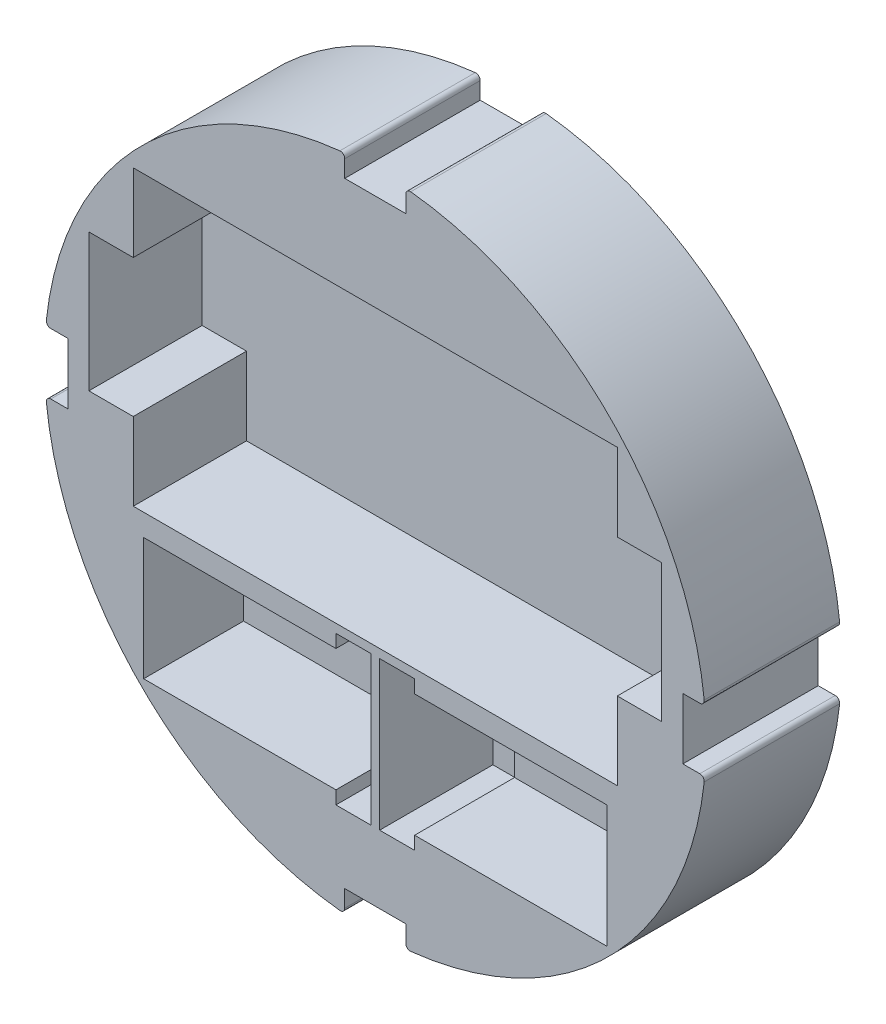
SolidWorks part; units mm, degrees
ref_plane "Front Plane" through (0, 0, 0) normal (0, 0, 1) x (1, 0, 0)
ref_plane "Top Plane" through (0, 0, 0) normal (0, 1, 0) x (1, 0, 0)
ref_plane "Right Plane" through (0, 0, 0) normal (1, 0, 0) x (0, 0, -1)
sketch "Sketch1" plane through (0, 0, 0) normal (0, 0, 1) x (1, 0, 0)
  line L0 (-1000, 0) -> (49000, 0) construction
  line L1 (6.985, -70.358) -> (-6.985, -70.358)
  line L6 (70.358, 6.985) -> (75.1332, 6.985)
  line L7 (70.358, 6.985) -> (70.358, -6.985)
  line L8 (70.358, -6.985) -> (75.1332, -6.985)
  line L9 (75.1332, 6.985) -> (75.1332, -6.985)
  line L10 (6.985, -70.358) -> (6.985, -75.1332)
  line L11 (6.985, -75.1332) -> (-6.985, -75.1332)
  line L12 (-6.985, -70.358) -> (-6.985, -75.1332)
  line L13 (-70.358, -6.985) -> (-70.358, 6.985)
  line L14 (-70.358, -6.985) -> (-75.1332, -6.985)
  line L15 (-75.1332, -6.985) -> (-75.1332, 6.985)
  line L16 (-70.358, 6.985) -> (-75.1332, 6.985)
  line L17 (-6.985, 70.358) -> (6.985, 70.358)
  line L18 (-6.985, 70.358) -> (-6.985, 75.1332)
  line L19 (-6.985, 75.1332) -> (6.985, 75.1332)
  line L20 (6.985, 70.358) -> (6.985, 75.1332)
  circle A0 centre (0, 0) radius 75.692 construction
  circle A1 centre (0, 0) radius 76.2 construction
  point P4 (70.358, 0)
  point P7 (0.442, 0)
  point P8 (0, 0)
  point P31 (0, 0)
  dimension "D1" = 151.384
  dimension "D2" = 152.4
  dimension "D3" = 13.97
  dimension "D4" = 140.716
  dimension "D6" = 4.7752
  dimension "D7" = 4
sketch "Sketch2" plane through (0, 0, 0) normal (0, 0, 1) x (1, 0, 0)
  line L0 (0, -1000) -> (0, 49000) construction
  line L1 (-55.372, 48.26) -> (55.372, 48.26)
  line L3 (-55.372, -18.796) -> (55.372, -18.796)
  line L4 (55.372, 48.26) -> (55.372, 30.48)
  line L5 (-201000, 0) -> (249000, 0) construction
  line L6 (55.372, 30.48) -> (65.532, 30.48)
  line L7 (65.532, 30.48) -> (65.532, -1.016)
  line L8 (65.532, -1.016) -> (55.372, -1.016)
  line L9 (55.372, -1.016) -> (55.372, -18.796)
  line L10 (-55.372, -1.016) -> (-55.372, -18.796)
  line L11 (-53, -23.796) -> (-9, -23.796)
  line L12 (-53, -23.796) -> (-53, -51.796)
  line L13 (-53, -51.796) -> (-9, -51.796)
  line L15 (-65.532, -1.016) -> (-55.372, -1.016)
  line L16 (-65.532, 30.48) -> (-65.532, -1.016)
  line L17 (-55.372, 48.26) -> (-55.372, 30.48)
  line L18 (-55.372, 30.48) -> (-65.532, 30.48)
  line L19 (-9, -23.796) -> (-9, -20.796)
  line L20 (-9, -20.796) -> (-1, -20.796)
  line L21 (-1, -20.796) -> (-1, -54.796)
  line L22 (-1, -54.796) -> (-9, -54.796)
  line L23 (-9, -54.796) -> (-9, -51.796)
  line L24 (53, -23.796) -> (9, -23.796)
  line L25 (9, -23.796) -> (9, -20.796)
  line L26 (9, -20.796) -> (1, -20.796)
  line L27 (1, -20.796) -> (1, -54.796)
  line L28 (1, -54.796) -> (9, -54.796)
  line L29 (9, -54.796) -> (9, -51.796)
  line L30 (53, -51.796) -> (9, -51.796)
  line L31 (53, -23.796) -> (53, -51.796)
  circle A0 centre (0, 0) radius 75.692 construction
  circle A1 centre (0, 0) radius 75.692
  point P7 (0, 48.26)
  dimension "D1" = 67.056
  dimension "D2" = 110.744
  dimension "D3" = 48.26
  dimension "D4" = 17.78
  dimension "D5" = 17.78
  dimension "D6" = 10.16
  dimension "D7" = 28
  dimension "D8" = 52
  dimension "D9" = 3
  dimension "D10" = 3
  dimension "D11" = 8
  dimension "D12" = 2
  dimension "D13" = 2
extrude "Boss-Extrude1" add sketch "Sketch2" along normal blind 25.908
sketch "Sketch3" plane through (0, 0, 0) normal (0, 0, -1) x (-1, 0, 0)
  circle A0 centre (0, 0) radius 75.692 construction
  circle A1 centre (0, 0) radius 75.692
extrude "Boss-Extrude2" add sketch "Sketch3" along normal blind 5.08
sketch "Sketch4" plane through (0, 0, 0) normal (0, 0, 1) x (1, 0, 0)
  line L1 (-53, -23.796) -> (-9, -23.796)
  line L2 (-53, -23.796) -> (-53, -51.796)
  line L3 (-53, -51.796) -> (-9, -51.796)
  line L4 (-9, -23.796) -> (-9, -51.796)
  line L5 (53, -23.796) -> (9, -23.796)
  line L6 (53, -23.796) -> (53, -51.796)
  line L7 (53, -51.796) -> (9, -51.796)
  line L8 (9, -23.796) -> (9, -51.796)
extrude "Boss-Extrude3" add sketch "Sketch4" along normal blind 3.048
sketch "Sketch7" plane through (0, 0, 25.908) normal (0, 0, 1) x (1, 0, 0)
  line L0 (6.985, 70.358) -> (-6.985, 70.358)
  line L1 (-6.985, 70.358) -> (-6.985, 75.369)
  line L2 (6.985, 70.358) -> (6.985, 75.369)
  line L3 (70.358, -6.985) -> (70.358, 6.985)
  line L4 (70.358, 6.985) -> (75.369, 6.985)
  line L5 (70.358, -6.985) -> (75.369, -6.985)
  line L6 (-6.985, -70.358) -> (6.985, -70.358)
  line L7 (6.985, -70.358) -> (6.985, -75.369)
  line L8 (-6.985, -70.358) -> (-6.985, -75.369)
  line L9 (-70.358, 6.985) -> (-70.358, -6.985)
  line L10 (-70.358, -6.985) -> (-75.369, -6.985)
  line L11 (-70.358, 6.985) -> (-75.369, 6.985)
  circle A0 centre (0, 0) radius 75.692 construction
  arc A1 (6.985, 75.369) -> (-6.985, 75.369) centre (0, 0) ccw
  arc A2 (75.369, -6.985) -> (75.369, 6.985) centre (0, 0) ccw
  arc A3 (-6.985, -75.369) -> (6.985, -75.369) centre (0, 0) ccw
  arc A4 (-75.369, 6.985) -> (-75.369, -6.985) centre (0, 0) ccw
  point P4 (0, 0)
  point P25 (0, 0)
  dimension "D1" = 4
extrude "Cut-Extrude1" cut sketch "Sketch7" against normal through all
fillet "Fillet1" radius 1.016 8 edges at (6.985, 75.369, 10.414) (-6.985, 75.369, 10.414) (75.369, -6.985, 10.414) (75.369, 6.985, 10.414) (-6.985, -75.369, 10.414) (6.985, -75.369, 10.414) (-75.369, 6.985, 10.414) (-75.369, -6.985, 10.414)
